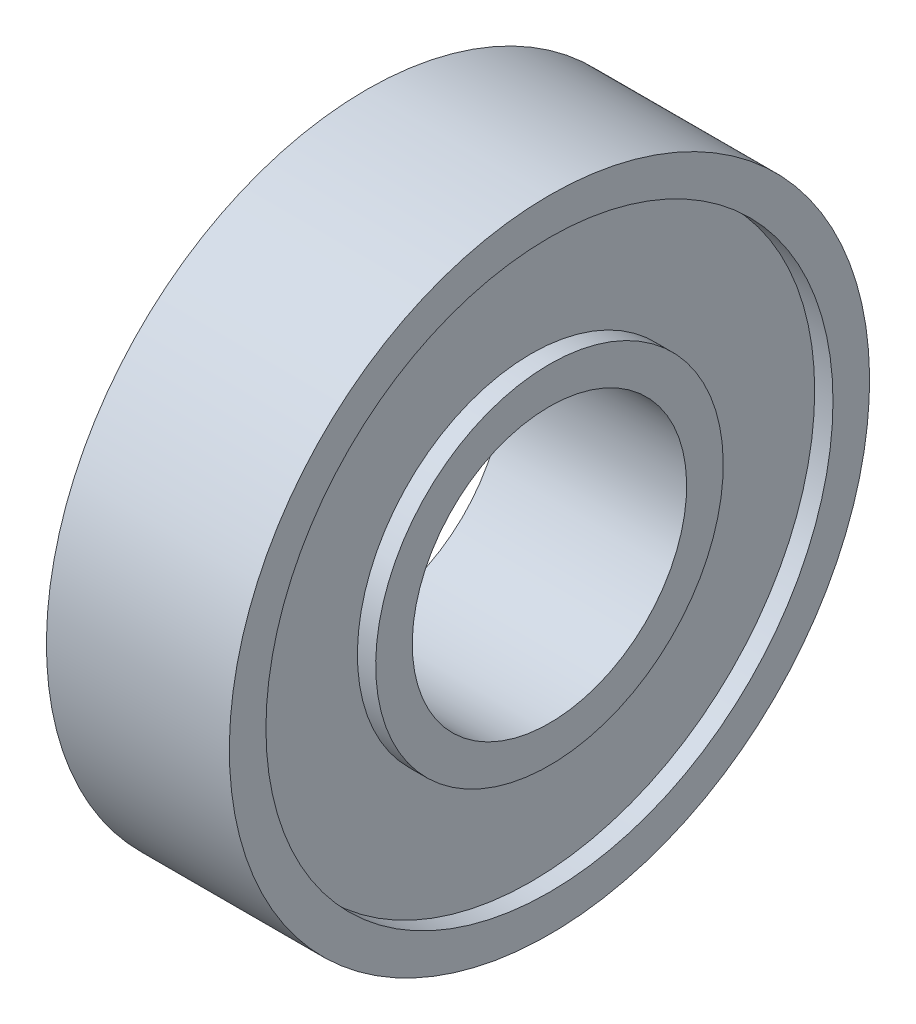
SolidWorks part; units mm, degrees
material "AISI 316 Stainless Steel Sheet (SS)"
ref_plane "Front Plane" through (0, 0, 0) normal (0, 0, 1) x (1, 0, 0)
ref_plane "Top Plane" through (0, 0, 0) normal (0, 1, 0) x (1, 0, 0)
ref_plane "Right Plane" through (0, 0, 0) normal (1, 0, 0) x (0, 0, -1)
sketch "Sketch1" plane through (0, 0, 0) normal (0, 0, 1) x (1, 0, 0)
  line L0 (6.4812, 0) -> (0, 0) construction
  line L1 (-4, 6) -> (4, 6)
  line L2 (4, 6) -> (4, 7.6)
  line L3 (4, 7.6) -> (3.2, 7.6)
  line L4 (3.2, 7.6) -> (3.2, 12.4)
  line L5 (3.2, 12.4) -> (4, 12.4)
  line L6 (4, 12.4) -> (4, 14)
  line L7 (4, 14) -> (-4, 14)
  line L8 (0, 14) -> (0, 6) construction
  line L9 (0, 6) -> (0, 0) construction
  line L10 (-4, 12.4) -> (-4, 14)
  line L11 (-3.2, 12.4) -> (-4, 12.4)
  line L12 (-3.2, 7.6) -> (-3.2, 12.4)
  line L13 (-4, 7.6) -> (-3.2, 7.6)
  line L14 (-4, 6) -> (-4, 7.6)
  line L15 (3.2, 12.4) -> (3.2, 13.2) construction
  line L16 (4, 12.4) -> (4, 10.8) construction
  line L17 (4, 10.8) -> (4, 9.2) construction
  line L18 (4, 9.2) -> (4, 7.6) construction
  point P21 (4, 13.2)
  dimension "D1" = 12
  dimension "D2" = 28
  dimension "D4" = 8
revolve "Revolve1" add sketch "Sketch1" angle 360 about L0
equation "\"d_i\"= 12"
equation "\"D1@Sketch1\"=\"d_i\""
equation "\"d_o\"= 28"
equation "\"w\"= 8"
equation "\"D4@Sketch1\"=\"w\""
equation "\"D2@Sketch1\"=\"d_o\""
